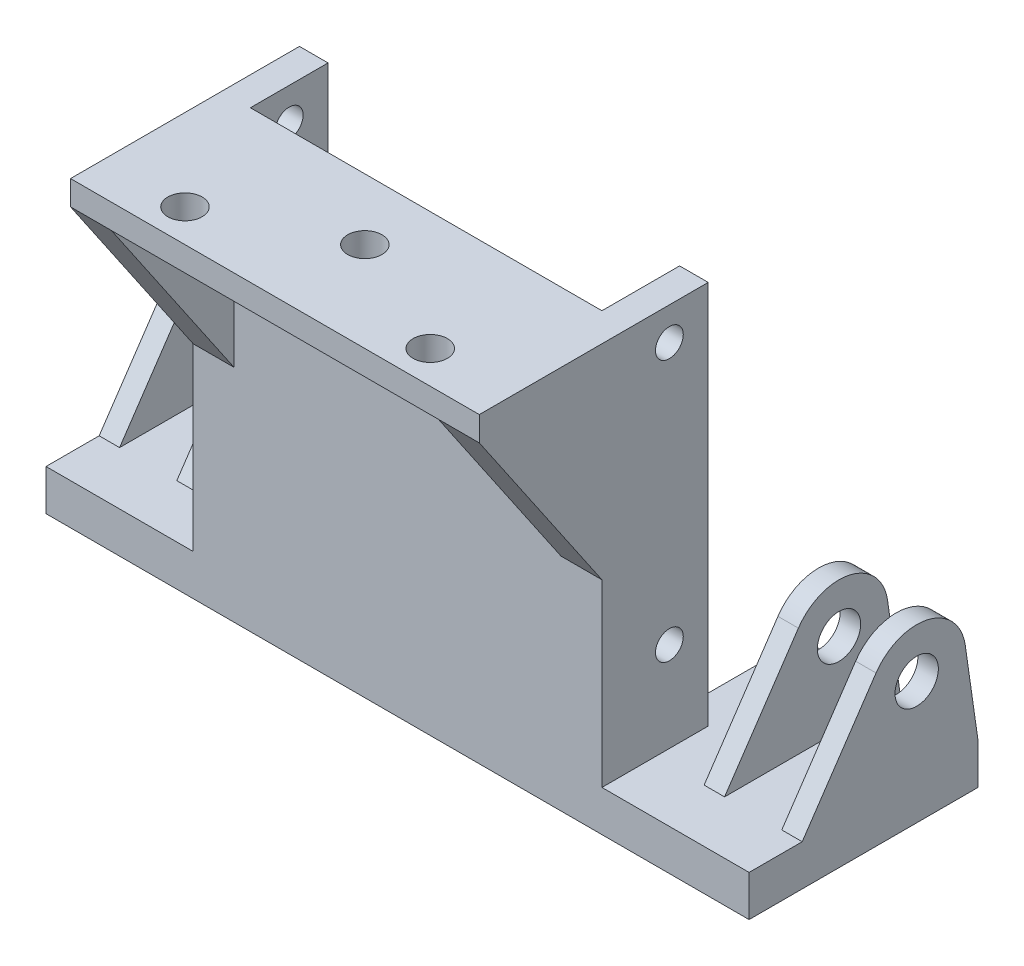
SolidWorks part; units mm, degrees
ref_plane "前视基准面" through (0, 0, 0) normal (0, 0, 1) x (1, 0, 0)
ref_plane "上视基准面" through (0, 0, 0) normal (0, 1, 0) x (1, 0, 0)
ref_plane "右视基准面" through (0, 0, 0) normal (1, 0, 0) x (0, 0, -1)
sketch "草图1" plane through (0, 0, 0) normal (0, 0, 1) x (1, 0, 0)
  line L0 (-25, 20) -> (-25, -20)
  line L1 (-25, 20) -> (25, 20)
  line L2 (25, 20) -> (25, -20)
  line L3 (25, -20) -> (-25, -20)
  line L4 (0, 0) -> (0, -20) construction
  line L5 (0, 0) -> (25, 0) construction
  dimension "D1" = 50
  dimension "D2" = 40
extrude "凸台-拉伸1" add sketch "草图1" along normal blind 5
sketch "草图2" plane through (0, 0, 0) normal (0, 0, -1) x (-1, 0, 0)
  line L0 (-19, -20) -> (-19, 20)
  line L1 (25, -20) -> (-25, -20) construction
  line L2 (-25, 20) -> (25, 20) construction
  line L3 (-19, 20) -> (-25, 20)
  line L4 (-25, 20) -> (-25, -20)
  line L5 (-25, -20) -> (-25, 20) construction
  line L6 (-25, -20) -> (-19, -20)
  line L7 (0, 20) -> (0, -20) construction
  line L8 (25, -20) -> (19, -20)
  line L9 (25, 20) -> (25, -20)
  line L10 (19, 20) -> (25, 20)
  line L11 (19, -20) -> (19, 20)
  dimension "D1" = 6
extrude "凸台-拉伸2" add sketch "草图2" along normal blind 8
sketch "草图4" plane through (0, 0, 0) normal (0, 0, -1) x (-1, 0, 0)
  line L0 (19, -20) -> (-19, -20) construction
  line L1 (19, 20) -> (19, -20) construction
  line L2 (-19, -20) -> (-19, 20) construction
  line L3 (-19, 20) -> (19, 20) construction
  line L4 (19, -20) -> (-19, -20)
  line L5 (19, 20) -> (19, -20)
  line L6 (-19, -20) -> (-19, 20)
  line L7 (-19, 20) -> (19, 20)
extrude "切除-拉伸2" cut sketch "草图4" against normal blind 1.5
sketch "草图6" plane through (-19, 0, 0) normal (1, 0, 0) x (0, 0, -1)
  line L0 (-1.5, 20) -> (-1.5, -20) construction
  line L1 (-1.5, -20) -> (8, -20) construction
  line L2 (8, -20) -> (8, 20) construction
  line L3 (8, 20) -> (-1.5, 20) construction
  line L4 (3.25, 20) -> (3.25, -20) construction
  line L5 (-1.5, 0) -> (8, 0) construction
  circle A0 centre (3.25, 16) radius 1.7
  circle A1 centre (3.25, -16) radius 1.7
  dimension "D1" = 3.4
  dimension "D2" = 16
extrude "切除-拉伸3" cut sketch "草图6" against normal through all both and the other way through all
sketch "草图7" plane through (0, -20, 0) normal (0, -1, 0) x (1, 0, 0)
  line L0 (21.5, -8) -> (21.5, 1.5)
  line L1 (25, -8) -> (19, -8) construction
  line L2 (21.5, 1.5) -> (-21.5, 1.5)
  line L3 (-21.5, 1.5) -> (-21.5, -8)
  line L4 (-19, -8) -> (-25, -8) construction
  line L5 (-21.5, -8) -> (21.5, -8)
  line L6 (25, 5) -> (25, -8) construction
  line L7 (-25, 5) -> (-25, -8) construction
  line L8 (19, 1.5) -> (-19, 1.5) construction
  dimension "D1" = 3.5
  dimension "D2" = 3.5
extrude "切除-拉伸4" cut sketch "草图7" against normal through all
sketch "草图8" plane through (0, 0, 5) normal (0, 0, 1) x (1, 0, 0)
  line L1 (-25, 20) -> (-25, -20) construction
  line L3 (25, -20) -> (25, 20) construction
  line L7 (-25, 0) -> (25, 0) construction
  line L8 (25, 20) -> (-25, 20)
  line L9 (25, 17) -> (25, 20)
  line L10 (-25, 17) -> (25, 17)
  line L11 (-25, 20) -> (-25, 17)
  dimension "D1" = 3
extrude "凸台-拉伸4" add sketch "草图8" along normal blind 15
sketch "草图9" plane through (0, 17, 0) normal (0, -1, 0) x (1, 0, 0)
  line L0 (-25, 20) -> (-25, 5) construction
  line L1 (25, 20) -> (25, 5) construction
  line L2 (-25, 20) -> (25, 20) construction
  line L3 (-25, 5) -> (25, 5) construction
  line L4 (0, 9) -> (0, 0) construction
  circle A0 centre (-15, 16) radius 2.1
  circle A1 centre (15, 16) radius 2.1
  circle A2 centre (0, 9) radius 2.1
  dimension "D1" = 4.2
  dimension "D2" = 10
  dimension "D3" = 10
  dimension "D4" = 4.2
  dimension "D5" = 4
  dimension "D6" = 4
  dimension "D7" = 4
extrude "切除-拉伸5" cut sketch "草图9" against normal through all
sketch "草图10" plane through (0, -20, 0) normal (0, -1, 0) x (1, 0, 0)
  line L8 (-25, -8) -> (-21.5, -8)
  line L9 (-21.5, -8) -> (-21.5, 1.5)
  line L10 (-21.5, 1.5) -> (21.5, 1.5)
  line L11 (21.5, 1.5) -> (21.5, -8)
  line L12 (21.5, -8) -> (25, -8)
  line L13 (25, -8) -> (25, 5)
  line L14 (25, 5) -> (-25, 5)
  line L15 (-25, 5) -> (-25, -8)
  line L16 (-25, -8) -> (-21.5, -8)
  line L17 (-21.5, -8) -> (-21.5, 1.5)
  line L18 (-21.5, 1.5) -> (21.5, 1.5)
  line L19 (21.5, 1.5) -> (21.5, -8)
  line L20 (21.5, -8) -> (25, -8)
  line L21 (25, -8) -> (25, 5)
  line L22 (25, 5) -> (-25, 5)
  line L23 (-25, 5) -> (-25, -8)
  dimension "D1" = 0
extrude "凸台-拉伸5" add sketch "草图10" along normal blind 12
sketch "草图11" plane through (25, 0, 0) normal (1, 0, 0) x (0, 0, -1)
  line L0 (-5, -32) -> (8, -32)
  line L1 (8, -32) -> (8, -27)
  line L2 (8, 20) -> (8, -32) construction
  line L3 (8, -27) -> (-5, -27)
  line L4 (-5, -32) -> (-5, 17) construction
  line L5 (-5, -27) -> (-5, -32)
  dimension "D1" = 5
extrude "凸台-拉伸6" add sketch "草图11" along normal blind 18
sketch "草图12" plane through (-25, 0, 0) normal (-1, 0, 0) x (0, 0, 1)
  line L0 (5, -32) -> (5, -27)
  line L1 (5, -27) -> (-8, -27)
  line L2 (-8, -27) -> (-8, -32)
  line L3 (-8, -32) -> (5, -32)
  dimension "D1" = 5
extrude "凸台-拉伸7" add sketch "草图12" along normal blind 18
sketch "草图13" plane through (0, 0, -8) normal (0, 0, -1) x (-1, 0, 0)
  line L0 (43, -32) -> (43, -27)
  line L1 (43, -27) -> (21.5, -27)
  line L2 (21.5, 20) -> (21.5, -32) construction
  line L3 (21.5, -27) -> (21.5, -32)
  line L4 (21.5, -32) -> (43, -32)
  line L5 (-21.5, -32) -> (-21.5, -27)
  line L6 (-21.5, 20) -> (-21.5, -32) construction
  line L7 (-21.5, -27) -> (-43, -27)
  line L8 (-43, -27) -> (-43, -32)
  line L9 (-43, -32) -> (-21.5, -32)
  line L10 (-21.5, -32) -> (-21.5574, -31.8951)
extrude "凸台-拉伸8" add sketch "草图13" along normal blind 15
sketch "草图18" plane through (-25, 0, 0) normal (-1, 0, 0) x (0, 0, 1)
  line L0 (5, -5) -> (20, 17)
  line L1 (5, 17) -> (5, -27) construction
  line L2 (20, 17) -> (5, 17) construction
  line L3 (20, 17) -> (5, 17)
  line L4 (5, 17) -> (5, -5)
extrude "凸台-拉伸11" add sketch "草图18" against normal blind 5
sketch "草图19" plane through (25, 0, 0) normal (1, 0, 0) x (0, 0, -1)
  line L0 (-5, 17) -> (-5, -5)
  line L1 (-5, -5) -> (-20, 17)
  line L2 (-20, 17) -> (-5, 17)
extrude "凸台-拉伸12" add sketch "草图19" against normal blind 5
sketch "草图20" plane through (-43, 0, 0) normal (-1, 0, 0) x (0, 0, 1)
  line L0 (-23, -27) -> (-21.4389, -16.1458)
  line L1 (-8, -27) -> (-23, -27) construction
  line L2 (-15.5, -27) -> (-15.5, -7.1022) construction
  line L3 (-1.5, -27) -> (-10.5288, -13.6403)
  line L4 (5, -27) -> (-8, -27) construction
  line L5 (-1.5, -27) -> (-23, -27)
  arc A0 (-10.5288, -13.6403) -> (-21.4389, -16.1458) centre (-15.5, -17) ccw
  circle A1 centre (-15.5, -17) radius 2.65
  dimension "D1" = 10
  dimension "D2" = 5.3
  dimension "D3" = 12
extrude "凸台-拉伸13" add sketch "草图20" against normal blind 12
sketch "草图21" plane through (0, 0, -23) normal (0, 0, -1) x (-1, 0, 0)
  line L0 (40.5, -27) -> (40.5, 7.1733)
  line L1 (43, -27) -> (31, -27) construction
  line L2 (40.5, 7.1733) -> (33.5, 7.1733)
  line L3 (33.5, 7.1733) -> (33.5, -27)
  line L4 (33.5, -27) -> (40.5, -27)
  dimension "D1" = 7
  dimension "D2" = 2.5
extrude "切除-拉伸8" cut sketch "草图21" against normal through all
mirror "镜向3" about plane through (0, 0, 0) normal (1, 0, 0) of "凸台-拉伸13", "切除-拉伸8"
